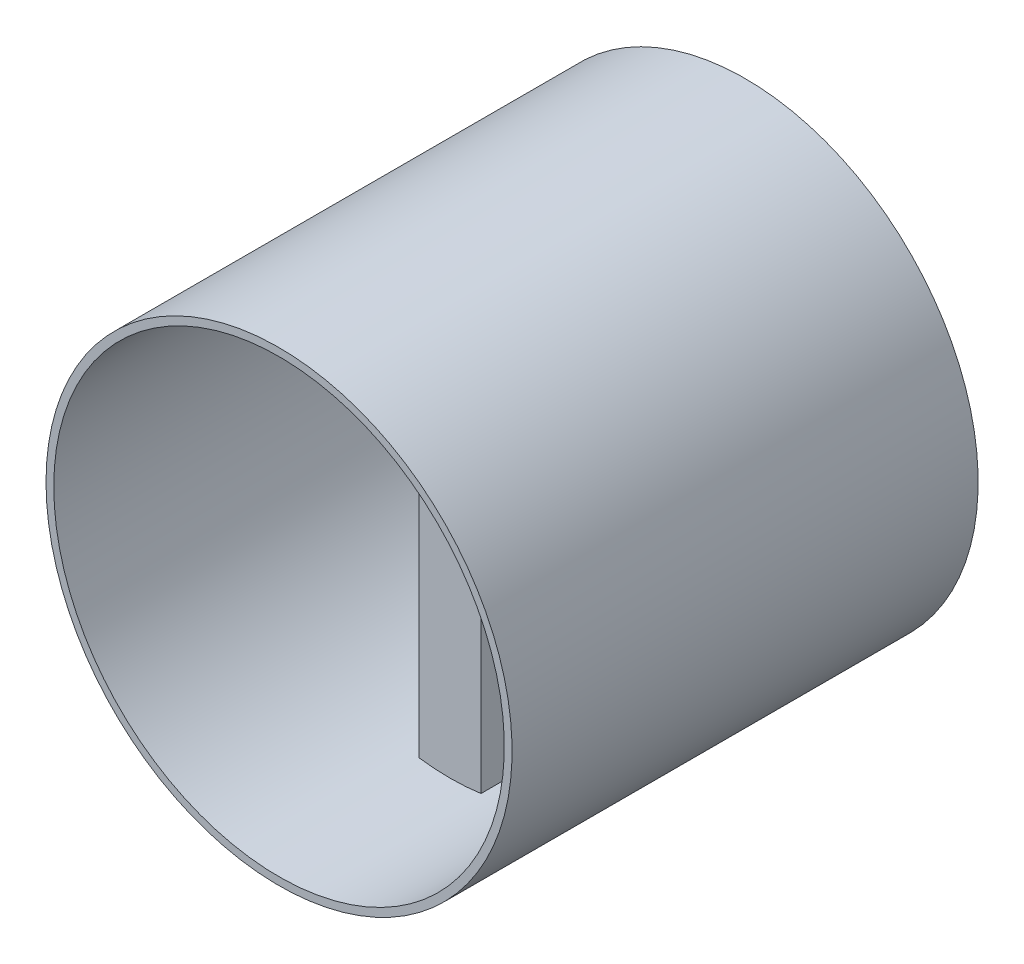
SolidWorks part; units mm, degrees
ref_plane "Plan de face" through (0, 0, 0) normal (0, 0, 1) x (1, 0, 0)
ref_plane "Plan de dessus" through (0, 0, 0) normal (0, 1, 0) x (1, 0, 0)
ref_plane "Plan de droite" through (0, 0, 0) normal (1, 0, 0) x (0, 0, -1)
sketch "Esquisse1" plane through (0, 0, 0) normal (0, 0, 1) x (1, 0, 0)
  line L1 (0, 0) -> (8, 0)
  line L2 (0, 0) -> (0, 59)
  line L3 (0, 59) -> (8, 59)
  line L4 (8, 0) -> (8, 59)
  dimension "D1" = 59
  dimension "D2" = 8
extrude "Boss.-Extru.1" add sketch "Esquisse1" along normal blind 60
sketch "Esquisse3" plane through (0, 0, 0) normal (0, 0, -1) x (-1, 0, 0)
  line L0 (-4, 59) -> (-4, 0) construction
  line L1 (-8, 59) -> (0, 59) construction
  line L2 (0, 0) -> (-8, 0) construction
  line L3 (0, 29.5) -> (-8, 29.5) construction
  line L4 (0, 59) -> (0, 0) construction
  line L5 (-8, 0) -> (-8, 59) construction
  circle A0 centre (-4, 29.5) radius 30
  circle A1 centre (-4, 29.5) radius 29
  dimension "D1" = 60
  dimension "D2" = 58
extrude "Boss.-Extru.2" add sketch "Esquisse3" against normal blind 60
sketch "Esquisse4" plane through (0, 0, 0) normal (0, 0, -1) x (-1, 0, 0)
  line L0 (-4, -0.5) -> (-4, 59.5) construction
  line L1 (-43.5151, 29.5) -> (32.2355, 29.5) construction
  circle A0 centre (-4, 29.5) radius 30 construction
  circle A5 centre (-4, 29.5) radius 29
  dimension "D1" = 58
extrude "Enlèv. mat.-Extru.3" cut sketch "Esquisse4" against normal blind 30
sketch "Esquisse5" plane through (0, 0, 30) normal (0, 0, -1) x (-1, 0, 0)
  line L0 (-4, 58.5) -> (-4, 0.5) construction
  line L1 (25, 29.5) -> (-33, 29.5) construction
  line L3 (-6, 43) -> (-6.9673, 29.942)
  line L5 (-6, 16) -> (-6.9673, 29.058)
  line L6 (-1.0327, 29.942) -> (-2, 43)
  line L7 (-2, 16) -> (-1.0327, 29.058)
  arc A0 (0, 58.2228) -> (-8, 58.2228) centre (-4, 29.5) ccw construction
  arc A1 (-8, 0.7772) -> (0, 0.7772) centre (-4, 29.5) ccw construction
  circle A2 centre (-4, 29.5) radius 29 construction
  arc A3 (-6.9673, 29.942) -> (-6.9673, 29.058) centre (-4, 29.5) ccw
  arc A4 (-2, 43) -> (-6, 43) centre (-4, 43) ccw
  arc A5 (-2, 16) -> (-6, 16) centre (-4, 16) cw
  arc A7 (-1.0327, 29.942) -> (-1.0327, 29.058) centre (-4, 29.5) cw
  dimension "D1" = 6
  dimension "D2" = 4
  dimension "D3" = 13.5
  dimension "D4" = 13.058
  dimension "D5" = 13.058
  dimension "D6" = 171.527
extrude "Enlèv. mat.-Extru.5" cut sketch "Esquisse5" against normal blind 1.5
sketch "Esquisse6" plane through (0, 0, 60) normal (0, 0, 1) x (1, 0, 0)
  line L0 (4, 59.5) -> (4, -0.5) construction
  line L1 (-25, 29.5) -> (33, 29.5) construction
  circle A0 centre (4, 29.5) radius 30 construction
  arc A1 (0, 58.2228) -> (0, 0.7772) centre (4, 29.5) ccw construction
  arc A2 (8, 0.7772) -> (8, 58.2228) centre (4, 29.5) ccw construction
  circle A3 centre (4, 29.5) radius 29
  dimension "D1" = 58
extrude "Enlèv. mat.-Extru.6" cut sketch "Esquisse6" against normal blind 22
sketch "Esquisse7" plane through (0, 0, 31.5) normal (0, 0, -1) x (-1, 0, 0)
  line L0 (-4, 45) -> (-4, 14) construction
  line L1 (-4, 14) -> (-33, 29.5) construction
  line L2 (-33, 29.5) -> (25, 29.5) construction
  arc A0 (-2, 43) -> (-6, 43) centre (-4, 43) ccw construction
  arc A1 (-6, 16) -> (-2, 16) centre (-4, 16) ccw construction
  circle A2 centre (-4, 29.5) radius 29 construction
  circle A3 centre (-4, 29.5) radius 2
  dimension "D1" = 4
extrude "Enlèv. mat.-Extru.7" cut sketch "Esquisse7" against normal blind 6.5
sketch "Esquisse8" plane through (0, 0, 31.5) normal (0, 0, -1) x (-1, 0, 0)
  line L0 (-4, 45) -> (-4, 14) construction
  line L1 (-33, 29.5) -> (25, 29.5) construction
  arc A0 (-2, 43) -> (-6, 43) centre (-4, 43) ccw construction
  arc A1 (-6, 16) -> (-2, 16) centre (-4, 16) ccw construction
  circle A2 centre (-4, 29.5) radius 29 construction
